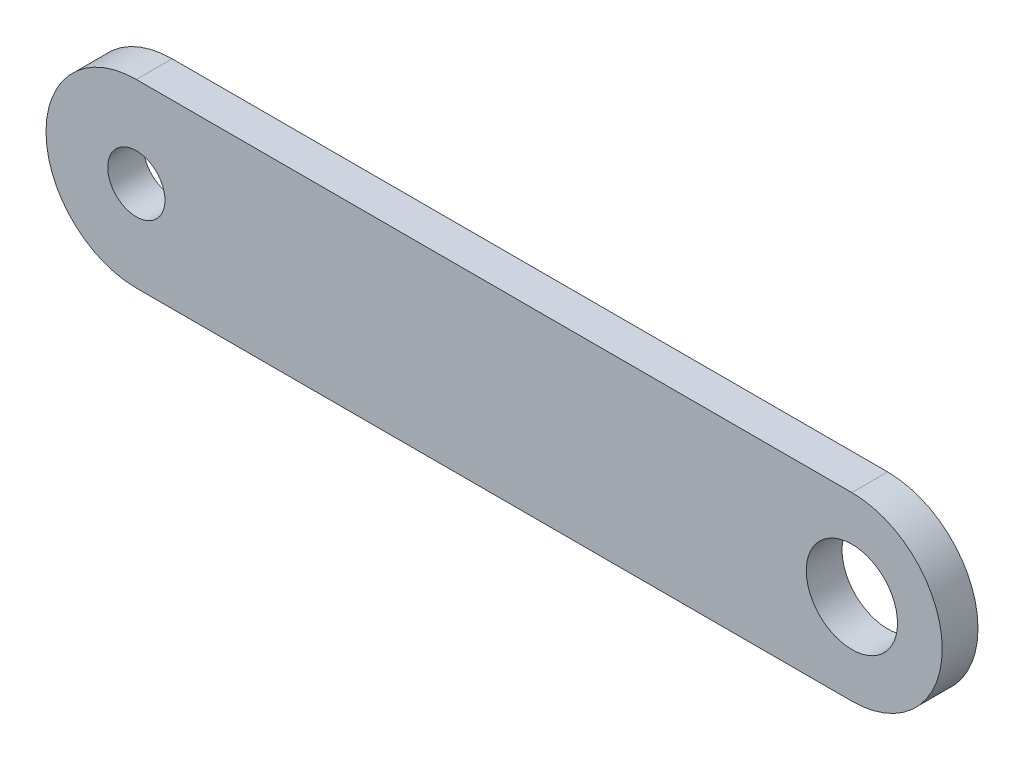
SolidWorks part; units mm, degrees
material "Thornel Mat VMA"
ref_plane "前视基准面" through (0, 0, 0) normal (0, 0, 1) x (1, 0, 0)
ref_plane "上视基准面" through (0, 0, 0) normal (0, 1, 0) x (1, 0, 0)
ref_plane "右视基准面" through (0, 0, 0) normal (1, 0, 0) x (0, 0, -1)
sketch "草图1" plane through (0, 0, 0) normal (0, 0, 1) x (1, 0, 0)
  line L0 (-20, 0) -> (20, 0) construction
  line L1 (-20, 0) -> (20, 0) construction
  line L2 (-20, 5.05) -> (20, 5.05)
  line L3 (-20, -5.05) -> (20, -5.05)
  circle A0 centre (-20, 0) radius 1.6
  circle A1 centre (20, 0) radius 2.55
  arc A2 (-20, 5.05) -> (-20, -5.05) centre (-20, 0) ccw
  arc A3 (20, -5.05) -> (20, 5.05) centre (20, 0) ccw
  point P5 (0, 0)
  dimension "D2" = 3.2
  dimension "D3" = 5.1
  dimension "D4" = 2.5
  dimension "D1" = 40
extrude "凸台-拉伸1" add sketch "草图1" along normal blind 2
